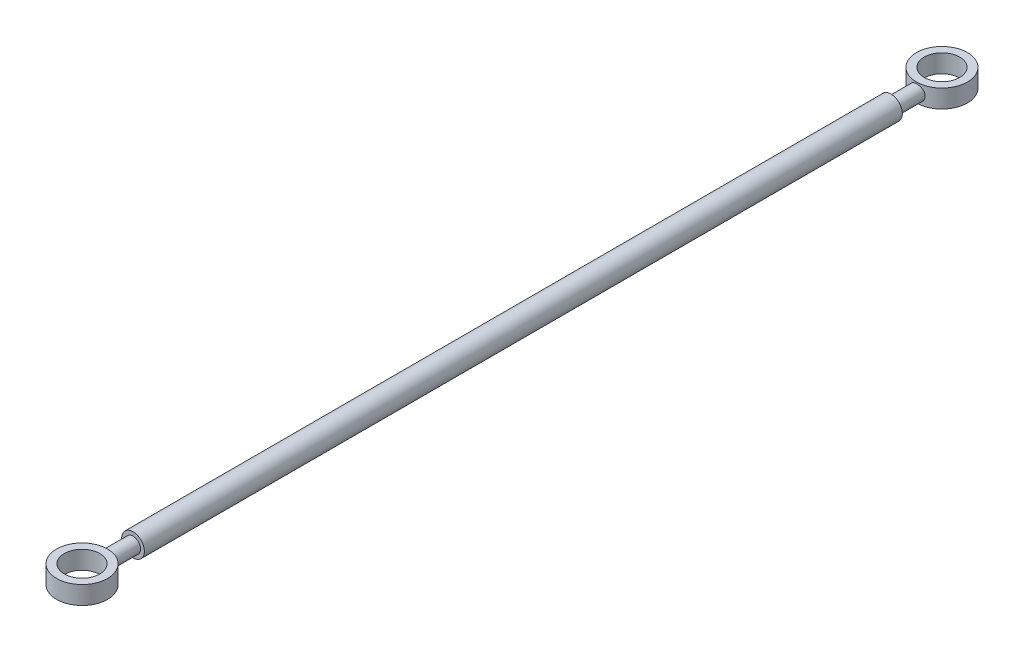
SolidWorks part; units mm, degrees
material "Hexcel AS4C (3000 필라멘트)"
ref_plane "정면" through (0, 0, 0) normal (0, 0, 1) x (1, 0, 0)
ref_plane "윗면" through (0, 0, 0) normal (0, 1, 0) x (1, 0, 0)
ref_plane "우측면" through (0, 0, 0) normal (1, 0, 0) x (0, 0, -1)
sketch "스케치1" plane through (0, 0, 0) normal (0, 1, 0) x (1, 0, 0)
  circle A0 centre (0, 0) radius 4.68
  circle A1 centre (0, 0) radius 6.725
  dimension "D1" = 9.36
  dimension "D2" = 13.45
extrude "보스-돌출1" add sketch "스케치1" along normal mid plane 4.8
ref_plane "평면1" through (0, 0, 113.45) normal (0, 0, 1) x (1, 0, 0)
sketch "스케치2" plane through (0, 0, 113.45) normal (0, 0, 1) x (1, 0, 0)
  circle A0 centre (0, 0) radius 2
  dimension "D1" = 4
extrude "보스-돌출2" add sketch "스케치2" against normal mid plane 215
sketch "스케치3" plane through (0, 0, 0) normal (0, 1, 0) x (1, 0, 0)
  circle A0 centre (0, 0) radius 4.675 construction
  dimension "D1" = 9.35
mirror "대칭 복사5" about plane through (0, 0, 113.45) normal (0, 0, 1) of "보스-돌출1"
sketch "스케치4" plane through (0, 0, 113.45) normal (0, 0, 1) x (1, 0, 0)
  circle A0 centre (0, 0) radius 3
  dimension "D1" = 6
extrude "보스-돌출3" add sketch "스케치4" along normal mid plane 200
sketch "스케치5" plane through (0, 0, 0) normal (0, 1, 0) x (1, 0, 0)
  circle A0 centre (0, -226.9) radius 4.675 construction
  dimension "D1" = 9.35
